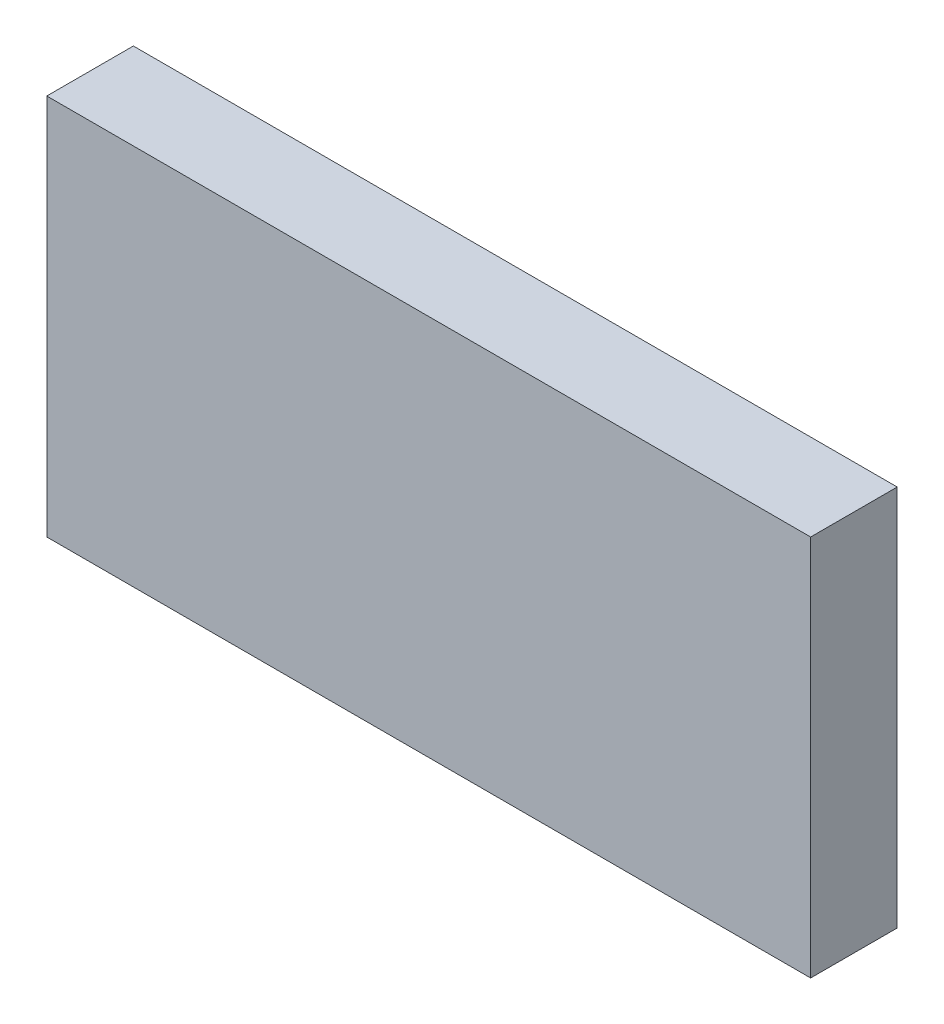
SolidWorks part; units mm, degrees
ref_plane "正面" through (0, 0, 0) normal (0, 0, 1) x (1, 0, 0)
ref_plane "平面" through (0, 0, 0) normal (0, 1, 0) x (1, 0, 0)
ref_plane "右側面" through (0, 0, 0) normal (1, 0, 0) x (0, 0, -1)
sketch "ｽｹｯﾁ1" plane through (0, 0, 0) normal (0, 0, 1) x (1, 0, 0)
  line L1 (0, 0) -> (30, 0)
  line L2 (0, 0) -> (0, 15)
  line L3 (0, 15) -> (30, 15)
  line L4 (30, 0) -> (30, 15)
  dimension "D1" = 30
  dimension "D2" = 15
extrude "ﾎﾞｽ - 押し出し1" add sketch "ｽｹｯﾁ1" along normal blind 3.4
